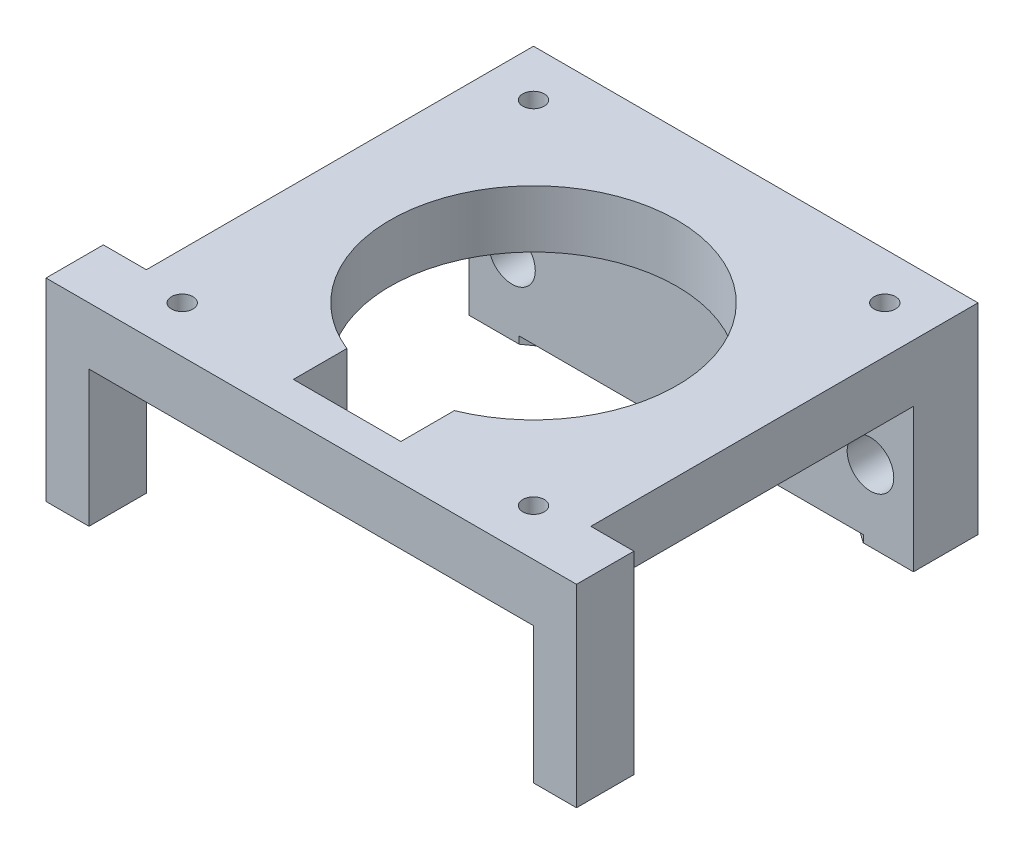
SolidWorks part; units mm, degrees
ref_plane "Front Plane" through (0, 0, 0) normal (0, 0, 1) x (1, 0, 0)
ref_plane "Top Plane" through (0, 0, 0) normal (0, 1, 0) x (1, 0, 0)
ref_plane "Right Plane" through (0, 0, 0) normal (1, 0, 0) x (0, 0, -1)
sketch "Sketch1" plane through (0, 0, 0) normal (0, 1, 0) x (1, 0, 0)
  line L0 (-15.5, 15.5) -> (15.5, -15.5) construction
  line L1 (-15.5, 15.5) -> (15.5, 15.5)
  line L2 (-15.5, 15.5) -> (-15.5, -15.5)
  line L3 (-15.5, -15.5) -> (15.5, -15.5)
  line L4 (15.5, 15.5) -> (15.5, -15.5)
  line L5 (-12.25, -12.25) -> (12.25, 12.25) construction
  line L6 (-12.25, 12.25) -> (12.25, 12.25) construction
  line L7 (-12.25, 12.25) -> (-12.25, -12.25) construction
  line L8 (-12.25, -12.25) -> (12.25, -12.25) construction
  line L9 (12.25, 12.25) -> (12.25, -12.25) construction
  circle A0 centre (-12.25, 12.25) radius 0.75
  circle A1 centre (12.25, 12.25) radius 0.75
  circle A2 centre (12.25, -12.25) radius 0.75
  circle A3 centre (-12.25, -12.25) radius 0.75
  circle A4 centre (0, 0) radius 10
  dimension "D3" = 1.5
  dimension "D4" = 20
  dimension "D1" = 31
  dimension "D2" = 24.5
extrude "Boss-Extrude1" add sketch "Sketch1" along normal blind 4
sketch "Sketch2" plane through (0, 0, 0) normal (0, -1, 0) x (1, 0, 0)
  line L0 (15.5, 15.5) -> (15.5, -15.5) construction
  line L1 (-15.5, -15.5) -> (15.5, -15.5)
  line L2 (-15.5, -15.5) -> (-15.5, -11)
  line L3 (-15.5, -11) -> (15.5, -11)
  line L4 (15.5, -15.5) -> (15.5, -11)
  dimension "D1" = 4.5
extrude "Boss-Extrude2" add sketch "Sketch2" along normal blind 10
sketch "Sketch3" plane through (0, 0, -11) normal (0, 0, 1) x (1, 0, 0)
  line L0 (0, 0) -> (0, -5) construction
  line L1 (12.5, -5) -> (-12.5, -5) construction
  circle A0 centre (-12.5, -5) radius 1.625
  circle A1 centre (12.5, -5) radius 1.625
  dimension "D3" = 3.25
  dimension "D1" = 25
  dimension "D2" = 5
extrude "Cut-Extrude1" cut sketch "Sketch3" against normal through all
sketch "Sketch4" plane through (0, 4, 0) normal (0, 1, 0) x (1, 0, 0)
  line L0 (0, 0) -> (0, -5) construction
  line L1 (-3.75, -5) -> (3.75, -5)
  line L2 (-3.75, -5) -> (-3.75, -13)
  line L3 (-3.75, -13) -> (3.75, -13)
  line L4 (3.75, -5) -> (3.75, -13)
  line L5 (-15.5, -15.5) -> (15.5, -15.5) construction
  dimension "D1" = 7.5
  dimension "D2" = 2.5
  dimension "D3" = 8
extrude "Cut-Extrude2" cut sketch "Sketch4" against normal through all
sketch "Sketch5" plane through (0, -10, 0) normal (0, -1, 0) x (1, 0, 0)
  line L0 (0, -15.5) -> (0, -15) construction
  line L1 (-15.5, -15.5) -> (15.5, -15.5) construction
  circle A0 centre (0, 5) radius 20
  dimension "D2" = 40
  dimension "D1" = 0.5
extrude "Cut-Extrude3" cut sketch "Sketch5" against normal blind 0.5
sketch "Sketch6" plane through (0, 4, 0) normal (0, 1, 0) x (1, 0, 0)
  line L1 (-15.5, -15.5) -> (-18.5, -15.5)
  line L2 (-15.5, -15.5) -> (-15.5, -11.5)
  line L3 (-15.5, -11.5) -> (-18.5, -11.5)
  line L4 (-18.5, -15.5) -> (-18.5, -11.5)
  line L5 (15.5, -15.5) -> (18.5, -15.5)
  line L6 (15.5, -15.5) -> (15.5, -11.5)
  line L7 (15.5, -11.5) -> (18.5, -11.5)
  line L8 (18.5, -15.5) -> (18.5, -11.5)
  dimension "D1" = 3
  dimension "D2" = 4
extrude "Boss-Extrude3" add sketch "Sketch6" against normal up to surface (13.5 mm away) up to face at (0, -9.5, -13)
